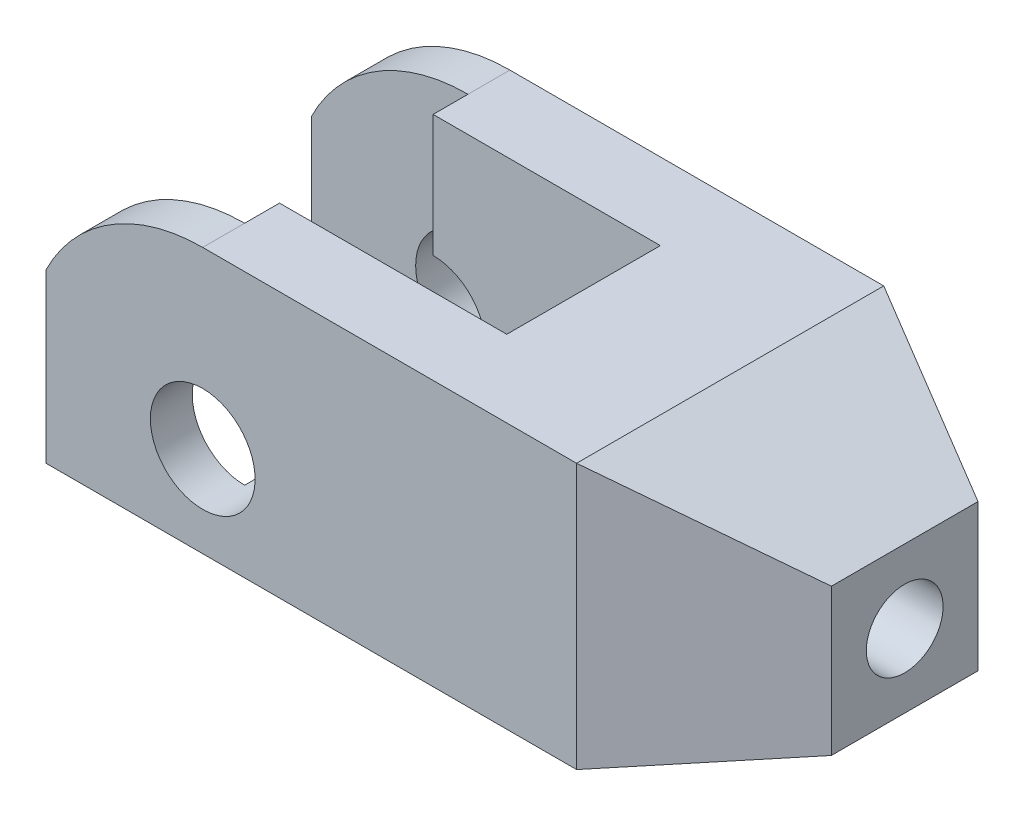
SolidWorks part; units mm, degrees
ref_plane "Front Plane" through (0, 0, 0) normal (0, 0, 1) x (1, 0, 0)
ref_plane "Top Plane" through (0, 0, 0) normal (0, 1, 0) x (1, 0, 0)
ref_plane "Right Plane" through (0, 0, 0) normal (1, 0, 0) x (0, 0, -1)
sketch "Sketch1" plane through (0, 0, 0) normal (0, 1, 0) x (1, 0, 0)
  line L1 (-38, -22) -> (38, -22)
  line L2 (-38, -22) -> (-38, 22)
  line L3 (-38, 22) -> (38, 22)
  line L4 (38, -22) -> (38, 22)
  line L5 (-38, -22) -> (38, 22) construction
  line L6 (-38, 22) -> (38, -22) construction
  point P0 (0, 0)
  dimension "D1" = 44
  dimension "D2" = 76
extrude "Boss-Extrude1" add sketch "Sketch1" along normal blind 38
sketch "Sketch2" plane through (0, 0, 22) normal (0, 0, 1) x (1, 0, 0)
  line L0 (-38, 38) -> (38, 38) construction
  line L13 (-38, 0) -> (38, 0)
  line L14 (38, 0) -> (38, 38)
  line L15 (38, 38) -> (-38, 38)
  line L16 (-38, 38) -> (-38, 0)
  line L19 (-15.5501, 38) -> (-38, 38)
  line L20 (-38, 38) -> (-38, 24)
  arc A0 (-15.5501, 38) -> (-38, 24) centre (-15.5501, 13) ccw
  circle A1 centre (-15.5501, 13) radius 7.5
  point P1 (-40.9957, 13)
  dimension "D1" = 50
  dimension "D2" = 15
  dimension "D3" = 0
  dimension "D4" = 24
extrude "Cut-Extrude1" cut sketch "Sketch2" against normal through all both and the other way through all
sketch "Sketch3" plane through (0, 38, 0) normal (0, 1, 0) x (1, 0, 0)
  line L0 (0, 0) -> (-51.1107, 0) construction
  line L1 (-38, 22) -> (-38, -22) construction
  line L2 (-38, 16) -> (-15.5501, 16)
  line L3 (-38, 16) -> (-38, -16)
  line L4 (-38, -16) -> (-15.5501, -16)
  line L5 (-15.5501, 16) -> (-15.5501, -16)
  line L6 (-15.5501, 22) -> (-15.5501, -22) construction
  line L7 (-15.5501, 11) -> (17, 11)
  line L8 (-15.5501, 11) -> (-15.5501, -11)
  line L9 (-15.5501, -11) -> (17, -11)
  line L10 (17, 11) -> (17, -11)
  dimension "D1" = 32
  dimension "D2" = 22
  dimension "D3" = 55
extrude "Cut-Extrude2" cut sketch "Sketch3" against normal through all both and the other way through all
ref_plane "Plane1" through (63, 0, 0) normal (1, 0, 0) x (0, 0, -1)
sketch "Sketch4" plane through (63, 0, 0) normal (1, 0, 0) x (0, 0, -1)
  line L0 (-22, 19) -> (0, 19) construction
  line L1 (-22, 38) -> (-22, 0) construction
  line L2 (0, 19) -> (0, 31.8666) construction
  line L4 (-10.5, 8.5) -> (10.5, 8.5)
  line L5 (-10.5, 8.5) -> (-10.5, 29.5)
  line L6 (-10.5, 29.5) -> (10.5, 29.5)
  line L7 (10.5, 8.5) -> (10.5, 29.5)
  line L8 (-10.5, 8.5) -> (10.5, 29.5) construction
  line L9 (-10.5, 29.5) -> (10.5, 8.5) construction
  dimension "D1" = 21
sketch "Sketch5" plane through (38, 0, 0) normal (1, 0, 0) x (0, 0, -1)
  line L4 (-22, 0) -> (22, 0)
  line L5 (22, 0) -> (22, 38)
  line L6 (22, 38) -> (-22, 38)
  line L7 (-22, 38) -> (-22, 0)
  line L8 (-22, 0) -> (22, 0)
  line L9 (22, 0) -> (22, 38)
  line L10 (22, 38) -> (-22, 38)
  line L11 (-22, 38) -> (-22, 0)
  dimension "D1" = 0
loft "Loft1" add profiles "Sketch5", "Sketch4"
sketch "Sketch6" plane through (63, 0, 0) normal (1, 0, 0) x (0, 0, -1)
  line L0 (-10.5, 29.5) -> (10.5, 8.5) construction
  circle A0 centre (0, 19) radius 5.5
  dimension "D1" = 11
extrude "Cut-Extrude3" cut sketch "Sketch6" against normal through all both and the other way through all
